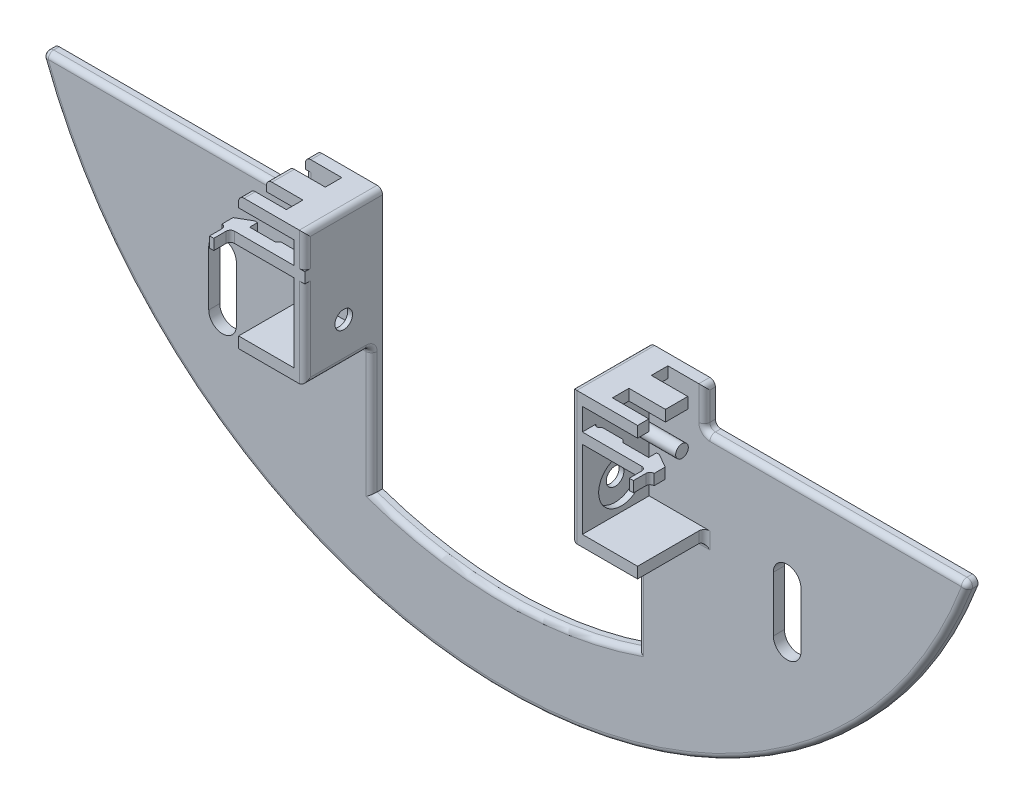
SolidWorks part; units mm, degrees
ref_plane "Front Plane" through (0, 0, 0) normal (0, 0, 1) x (1, 0, 0)
ref_plane "Top Plane" through (0, 0, 0) normal (0, 1, 0) x (1, 0, 0)
ref_plane "Right Plane" through (0, 0, 0) normal (1, 0, 0) x (0, 0, -1)
sketch "Sketch1" plane through (0, 0, 0) normal (0, 0, 1) x (1, 0, 0)
  line L0 (24.15, -30.4) -> (24.15, -23.3309)
  line L2 (24.15, -23.3309) -> (36.15, -23.3309)
  line L3 (-20.7971, -18) -> (20.7971, -18) construction
  line L4 (36.15, -23.3309) -> (36.15, -30.4)
  line L6 (-20.7971, -30.4) -> (20.7971, -30.4) construction
  line L7 (16, -30.4) -> (-16, -30.4) construction
  line L8 (0, -18) -> (0, -30.4) construction
  line L9 (-24.15, -30.4) -> (-24.15, -23.3309)
  line L10 (-24.15, -23.3309) -> (-36.15, -23.3309)
  line L11 (-36.15, -23.3309) -> (-36.15, -30.4)
  line L13 (36.15, -30.4) -> (84.1789, -30.4)
  line L14 (-36.15, -30.4) -> (-84.1789, -30.4)
  line L15 (-24.15, -30.4) -> (-24.15, -70.4771)
  line L16 (24.15, -30.4) -> (24.15, -70.4771)
  line L17 (20, -46.2619) -> (20, -34.4) construction
  circle A6 centre (0, 0) radius 89.5
  arc A7 (-84.1789, -30.4) -> (84.1789, -30.4) centre (0, 0) ccw
  arc A13 (-24.15, -70.4771) -> (24.15, -70.4771) centre (0, 0) ccw
  arc A39 (-7.5, 16.3631) -> (7.5, 16.3631) centre (0, 0) ccw construction
  point P13 (-65.8932, -25.0667)
  point P14 (0, -18)
  point P17 (0, -30.4)
  point P22 (65.8932, -25.0667)
  point P31 (20, -40.3309)
  dimension "D3" = 4.15
  dimension "irBeamUnitWidth" = 12
  dimension "D4" = 15
  dimension "irBeamUnitLEDDistanceFromBottom" = 17
  dimension "D1" = 26
extrude "Boss-Extrude1" add sketch "Sketch1" along normal blind 2
sketch "Sketch3" plane through (0, 0, 2) normal (0, 0, -1) x (-1, 0, 0)
  line L0 (26.15, -45.4309) -> (26.15, -25.3309)
  line L1 (26.15, -25.3309) -> (36.15, -25.3309)
  line L2 (24.15, -23.3309) -> (36.15, -23.3309) construction
  line L3 (24.15, -70.4771) -> (24.15, -23.3309) construction
  line L4 (24.15, -23.3309) -> (36.15, -23.3309)
  line L5 (24.15, -47.4309) -> (24.15, -23.3309)
  line L7 (36.15, -23.3309) -> (36.15, -30.4) construction
  line L8 (36.15, -23.3309) -> (36.15, -25.3309)
  line L9 (-36.15, -47.4309) -> (-24.15, -47.4309)
  line L10 (0, 0) -> (0, -125.7174) construction
  line L11 (26.15, -45.4309) -> (36.15, -45.4309)
  line L12 (36.15, -45.4309) -> (36.15, -47.4309)
  line L13 (36.15, -47.4309) -> (24.15, -47.4309)
  line L14 (-36.15, -45.4309) -> (-36.15, -47.4309)
  line L15 (-26.15, -45.4309) -> (-36.15, -45.4309)
  line L16 (-36.15, -23.3309) -> (-36.15, -25.3309)
  line L17 (-24.15, -47.4309) -> (-24.15, -23.3309)
  line L18 (-24.15, -23.3309) -> (-36.15, -23.3309)
  line L19 (-26.15, -25.3309) -> (-36.15, -25.3309)
  line L20 (-26.15, -45.4309) -> (-26.15, -25.3309)
  dimension "D1" = 2
  dimension "D2" = 2
  dimension "D3" = 2
  dimension "irBeamUnitLength" = 20.1
extrude "Boss-Extrude2" add sketch "Sketch3" against normal blind 12.1
sketch "Sketch4" plane through (26.15, 0, 0) normal (1, 0, 0) x (0, 0, -1)
  line L0 (-2, -30.4) -> (-2, -89.5) construction
  line L3 (-14.1, -25.3309) -> (-2, -25.3309) construction
  circle A0 centre (-7.05, -40.3809) radius 4.1
  dimension "irBeamUnitLEDMountDiameter" = 8.2
  dimension "irBeamUnitLEDDistanceFromBottom" = 15.05
  dimension "irBeamUnitWidth" = 5.05
extrude "Cut-Extrude1" cut sketch "Sketch4" against normal blind 1.12
sketch "Sketch5" plane through (25.03, 0, 0) normal (1, 0, 0) x (0, 0, -1)
  line L0 (-2, -30.4) -> (-2, -89.5) construction
  line L1 (-14.1, -25.3309) -> (-2, -25.3309) construction
  circle A0 centre (-7.05, -40.3809) radius 1.6
  dimension "irBeamUnitWidth" = 5.05
  dimension "irBeamUnitLEDDiameter" = 3.2
  dimension "irBeamUnitLEDDistanceFromBottom" = 15.05
extrude "Cut-Extrude2" cut sketch "Sketch5" against normal up to surface (49.18 mm away)
sketch "Sketch6" plane through (26.15, 0, 0) normal (1, 0, 0) x (0, 0, -1)
  line L1 (-14.1, -25.3309) -> (-2, -25.3309) construction
  line L2 (-2, -30.4) -> (-2, -25.3309) construction
  circle A0 centre (-7.05, -30.3809) radius 1.15
  dimension "irBeamUnitWidth" = 5.05
  dimension "irBeamUnitMountHoleDiameter" = 2.3
  dimension "irBeamUnitMountHoleDistanceFromBottom" = 5.05
extrude "Boss-Extrude3" add sketch "Sketch6" along normal blind 11
sketch "Sketch8" plane through (0, 0, 14.1) normal (0, 0, 1) x (1, 0, 0)
  line L0 (24.15, -47.4309) -> (24.15, -23.3309) construction
  line L1 (24.15, -31.2909) -> (24.15, -29.3609)
  line L2 (24.15, -29.3609) -> (39.15, -29.3609)
  line L3 (39.15, -29.3609) -> (39.15, -31.2909)
  line L4 (39.15, -31.2909) -> (24.15, -31.2909)
  line L5 (36.15, -25.3309) -> (26.15, -25.3309) construction
  dimension "irBeamUnitSideSlotsDistanceFromBottom" = 4.03
  dimension "irBeamUnitSlotWidth" = 1.93
  dimension "irBeamUnitHeight" = 15
extrude "Boss-Extrude4" add sketch "Sketch8" against normal blind 2
sketch "Sketch9" plane through (0, -31.2909, 0) normal (0, -1, 0) x (1, 0, 0)
  line L0 (36.15, 12.1) -> (36.15, 10.6566)
  line L1 (26.15, 12.1) -> (39.15, 12.1) construction
  line L2 (36.15, 10.6566) -> (36.65, 10.6566)
  line L3 (36.65, 10.6566) -> (39.15, 12.1)
  line L5 (26.15, 12.1) -> (31.51, 12.1)
  line L6 (31.51, 12.1) -> (31, 11.59)
  line L9 (36.15, 12.1) -> (39.15, 12.1)
  line L10 (26.15, 14.1) -> (26.15, 12.1) construction
  line L12 (26.15, 12.1) -> (26.15, 11.59)
  line L13 (31, 11.59) -> (27.2589, 11.59)
  line L14 (27.2589, 11.59) -> (26.9954, 11.8536)
  line L15 (26.9972, 12) -> (26.2772, 12) construction
  line L17 (26.15, 14.1) -> (39.15, 14.1) construction
  line L22 (38.4, 14.85) -> (38.4, 17.1)
  line L23 (37.65, 17.1) -> (38.4, 17.1)
  line L24 (37.65, 17.1) -> (37.65, 14.85)
  line L25 (36.9, 14.1) -> (39.15, 14.1)
  arc A0 (26.9954, 11.8536) -> (26.15, 11.59) centre (26.6418, 11.5) ccw
  arc A1 (39.15, 14.1) -> (38.4, 14.85) centre (39.15, 14.85) cw
  arc A2 (37.65, 14.85) -> (36.9, 14.1) centre (36.9, 14.85) cw
  dimension "D7" = 0.5
  dimension "D10" = 0.75
  dimension "D1" = 45
  dimension "D2" = 4.85
  dimension "D4" = 10
  dimension "D5" = 0.5
  dimension "D3" = 0.51
  dimension "D6" = 60
  dimension "D8" = 0.1
  dimension "D9" = 0.75
  dimension "D11" = 3
extrude "Boss-Extrude5" add sketch "Sketch9" against normal up to surface (1.93 mm away) up to face at (32.65, -29.3609, 13.1)
sketch "Sketch10" plane through (0, -25.3309, 0) normal (0, -1, 0) x (1, 0, 0)
  line L0 (36.15, 14.1) -> (36.15, 2) construction
  line L1 (36.15, 12.05) -> (36.15, 9.05)
  line L2 (36.15, 2) -> (29.54, 2)
  line L3 (36.15, 2) -> (26.15, 2) construction
  line L4 (29.54, 2) -> (29.54, 5)
  line L7 (26.15, 14.1) -> (26.15, 2) construction
  line L8 (29.54, 9.05) -> (36.15, 9.05)
  line L9 (29.54, 5) -> (36.15, 5)
  line L10 (36.15, 12.05) -> (29.54, 12.05)
  line L11 (29.54, 12.05) -> (29.54, 9.05)
  line L12 (36.15, 5) -> (36.15, 2)
  line L14 (36.15, 14.1) -> (26.15, 14.1) construction
  dimension "irBeamUnitHeight" = 3.39
  dimension "D2" = 3
  dimension "D3" = 3
  dimension "irBeamUnitMountingPlateThickness" = 2.05
extrude "Cut-Extrude3" cut sketch "Sketch10" against normal through all
fillet "Fillet1" radius 1 24 edges at (36.15, -23.3309, 1) (-60.1645, -30.4, 2) (24.15, -23.3309, 7.05) (36.15, -30.4, 1) (84.1789, -30.4, 1) (-84.1789, -30.4, 1) (-36.15, -30.4, 1) (-36.15, -23.3309, 7.05) (-24.15, -23.3309, 7.05) (0, -89.5, 2) (60.1645, -30.4, 2) (36.15, -26.8655, 2) (-36.15, -27.8655, 2) (-24.15, -35.3809, 14.1) (-24.15, -47.4309, 8.05) (-30.15, -47.4309, 2) (-36.15, -46.4309, 2) (0, -74.5, 2) (-24.15, -58.954, 2) (24.15, -58.954, 2) (24.15, -35.3809, 14.1) (24.15, -47.4309, 8.05) (36.15, -46.4309, 2) (30.15, -47.4309, 2)
hole_wizard "Ø5.0mm Dowel Hole1" positions "Sketch16" profile "Sketch17" hole size "Ø5.0" standard "ANSI Metric" end condition through all
sketch "Sketch16" plane through (0, 0, -31.1) normal (0, 0, -1) x (-1, 0, 0)
  point P0 (-51.1598, -51.1598)
  point P3 (51.1598, -51.1598)
  point P6 (51.1598, 51.1598)
  point P9 (-51.1598, 51.1598)
sketch "Sketch17" plane through (51.1598, -51.1598, -31.1) normal (1, 0, 0) x (0, 1, 0)
  line L0 (0, 0) -> (0, 48.2)
  line L1 (0, 48.2) -> (2.5, 48.2)
  line L2 (2.5, 48.2) -> (2.5, 0)
  line L3 (2.5, 0) -> (0, 0)
  line L4 (0, -6.35) -> (0, 107.95) construction
  dimension "Thru Hole Dia." = 5
  dimension "Thru Hole Depth" = 48.2
sketch "Sketch13" plane through (0, 0, 2) normal (0, 0, 1) x (1, 0, 0)
  line L0 (51.1598, -46.1598) -> (51.1598, -56.1598) construction
  line L1 (53.6598, -46.1598) -> (53.6598, -56.1598)
  line L2 (48.6598, -46.1598) -> (48.6598, -56.1598)
  arc A0 (53.6598, -46.1598) -> (48.6598, -46.1598) centre (51.1598, -46.1598) ccw
  arc A1 (48.6598, -56.1598) -> (53.6598, -56.1598) centre (51.1598, -56.1598) ccw
  circle A6 centre (51.1598, -51.1598) radius 2.5 construction
  point P2 (51.1598, -51.1598)
  dimension "irBeamUnitMountingPlateAdjustmentSlotLength" = 10
extrude "Cut-Extrude4" cut sketch "Sketch13" against normal through all
mirror "Mirror1" about plane through (0, 0, 0) normal (1, 0, 0) of "Cut-Extrude4", "Cut-Extrude2", "Boss-Extrude3", "Boss-Extrude4", "Boss-Extrude5", "Cut-Extrude3", "Cut-Extrude1"
equation "\"D1@Sketch1\"=\"motorMountOffset\"-\"hopperBaseLipOverhang\"+1"
equation "\"D3@Sketch1\"=(\"irBeamUnitLEDDomeSectionDiameter\"/2) + \"irBeamUnitLEDFlatSectionHeight\" + 2mm"
equation "\"pelletWidth\"= 13mm'The Width of the pellet to be dispensed"
equation "\"pelletLength\"= 26mm'The length of the pellet to be dispensed"
equation "\"pelletThickness\"= 13mm'The Thickness of the pellet to be dispensed"
equation "\"pelletRadius\"= 10mm'The roundness / radius of the pellet to be dispensed"
equation "\"rotatingPlateDiameter\"= 100mm'the diameter of the rotating plate"
equation "\"rotatingPlateHeight\"= (\"pelletThickness\"*0.9)'The thickness of the rotating plate"
equation "\"rotatingPlateDiameterAllowance\"= 0.5mm'Allowance around the edge of the rotating plate"
equation "\"rotatingPlatePelletSlotLength\"= \"pelletLength\"*1.3'The length of the slot where a pellet will be captured"
equation "\"rotatingPlatePelletSlotWidth\"= \"pelletWidth\"*1.3'The width of the slot where a pellet will be captured"
equation "\"rotatingPlateNumberOfPelletSlots\"= ( (2*pi*(\"rotatingPlateDiameter\"/2)) / ((\"rotatingPlatePelletSlotLength\"*1.1)*3) )'The maximum number of pellet slots allows in the rotating plate for proper spacing"
equation "\"rotatingPlateAgitatorDiameter\"= ( \"rotatingPlateDiameter\"-((\"pelletWidth\"*1.3)*2.5) )'The diameter of the \"agitator\" section of the rotating plate"
equation "\"rotatingPlateAgitatorHeight\"= 80mm'The height of the \"agitator\" section of the rotating plate"
equation "\"rotatingPlateAgitatorTopRoundingRadius\"= 6mm'The rounding radius of the top of the \"agitator\" section of the rotating plate"
equation "\"rotatingPlateAgitatorBladeThickness\"= 4mm'The thickness of the blade on the \"agitator\" section of the rotating plate"
equation "\"rotatingPlateAgitatorBladeDistance\"= ( (\"rotatingPlateAgitatorDiameter\"+ 20mm) - (\"rotatingPlateAgitatorDiameter\") )'The distance offset of the blade from the surface of the \"agitator\" section of the rotating plate"
equation "\"rotatingPlateAgitatorBladeBottomGap\"= ( \"pelletThickness\"*1.2 )'The gap between the bottom of the blade and the base of the plate on the \"agitator\" section of the rotating plate"
equation "\"rotatingPlateAgitatorBladesNumber\"= ( 3 )'The number of blades on the \"agitator\" section of the rotating plate"
equation "\"hopperBaseInnerDiameter\"= (\"rotatingPlateDiameter\") + (\"rotatingPlateDiameterAllowance\"*2)'Diameter of the Base of the hopper where it meets the motor mount + rotating plate"
equation "\"hopperBaseOuterDiameter\"= (\"hopperBaseInnerDiameter\" + (\"hopperTankWallThickness\"*2) + 60mm)'Diameter of the Base of the hopper where it meets the motor mount + rotating plate"
equation "\"hopperBaseChamferAngle\"= 60deg'Angle of the chamfer of the Hopper base Toward the plate"
equation "\"hopperBaseLipOverhang\"= 5mm'The overhang amount of the hopper base lip"
equation "\"hopperBaseLipDepth\"= 5mm'The depth of the hopper base's overhang lip"
equation "\"hopperBaseLockNotchWidth\"= 10mm'The width of the hopper base \"lock\" notch to prevent rotation"
equation "\"hopperBaseLockNotchHeight\"= 10mm'The height of the hopper base \"lock\" notch to prevent rotation"
equation "\"hopperBaseRearNotchHeight\"= 8mm'The height of the rear snap-lock notch on the hopper base"
equation "\"hopperBaseRearNotchWidth\"= 8mm'The width of the rear snap-lock notch on the hopper base"
equation "\"hopperTankWallThickness\"= 5mm'The wall thickness of the hopper tank where pellet reserve will be stored"
equation "\"hopperTankDiameter\"= ( \"rotatingPlateDiameter\"*1.8 )'**Must be greater than \"rotatingPlateDiameter\" -- The inner diameter of the hopper tank where pellet reserve will be stored"
equation "\"hopperTankHeight\"= 200mm'The height of the hopper tank where pellet reserve will be stored"
equation "\"hopperTankCoverThickness\"= 10mm'The thickness of the Hopper Tank's cover"
equation "\"hopperTankCoverHandleLength\"= 60mm'The length of the handles on the hopper tank cover"
equation "\"hopperTankCoverHandleWidth\"= 20mm'The width of the handles on the hopper tank cover, defined as the offset from the cover's main edge"
equation "\"motorMountOffset\"= 30mm'The distance offset of the motor mount part from the hopper tank's outer edge"
equation "\"motorMountHeight\"= (\"motorHeight\" + \"motorFacePlateThickness\" + 0mm)'The height / thickness of the motor mount part"
equation "\"motorMountPelletThroughHoleLength\"= 40mm'The length of the pellet throughhole that routes through the motor mount and other parts"
equation "\"motorMountPelletThroughHoleWidth\"= 20mm'The width of the pellet throughhole that routes through the motor mount and other parts"
equation "\"motorDiameter\"= 35mm'The Diameter of the main motor unit"
equation "\"motorHeight\"= 13.4mm'The height of the main motor unit"
equation "\"motorConnectorWidth\"= 10mm'The width of the motor's electrical cable connector"
equation "\"motorConnectorLength\"= 8mm'The length of the motor's electrical cable connector"
equation "\"motorConnectorHeight\"= 5mm'The height of the motor's electrical cable connector"
equation "\"motorFacePlateLength\"= 50mm'The length of the motor faceplate"
equation "\"motorFacePlateWidth\"= 10mm'The width of the motor faceplate"
equation "\"motorFacePlateThickness\"= 1mm'The thickness of the motor faceplate"
equation "\"motorFacePlateCenterRadius\"= 20mm'The rounding radius of the motor faceplate center"
equation "\"motorFacePlateEndRadius\"= 10mm'The rounding radius of the motor faceplate ends"
equation "\"motorFacePlateMountingHoleDiameter\"= 6mm'The diameter of the motor faceplate's mounting holes"
equation "\"motorFacePlateMoutingHoleDistanceBetweenHoles\"= 42mm'The distance between the center of the mounting holes"
equation "\"motorSpindleDiameter\"= 2mm'The diameter of the motor spindle"
equation "\"motorSpindleFlatFaceLength\"= 1.5mm'The length of the flat face of the motor spindle"
equation "\"motorSpindleHeight\"= 9mm'The height of the motor spindle from the face of the motor"
equation "\"motorSpindleMountDiameter\"= 12mm'The diameter of the raised mount section of the motor where the spindle is attached"
equation "\"motorSpindleMountHeight\"= 1.5mm'The height of the raised mount section of the motor where the spindle is attached"
equation "\"irBeamUnitLength\"=20mm'The legth of the IR beam unit"
equation "\"irBeamUnitWidth\"=10mm'The width of the IR beam unit"
equation "\"irBeamUnitHeight\"=8mm'The height of the IR beam unit"
equation "\"irBeamUnitSlotWidth\"=2.03mm'The width of the slots on the outside of the IR beam unit"
equation "\"irBeamUnitSlotDepth\"=0.76mm'The depth of the slots on the outside of the IR beam unit"
equation "\"irBeamUnitSideSlotsDistanceFromBottom\"=3.98mm'The distance of the side slots on the outside of the IR beam unit from the bottom edge of the unit"
equation "\"irBeamUnitMountHoleDistanceFromBottom\"=5mm'The distance of the center mounting throughhole of the IR beam unit from the bottom edge of the unit"
equation "\"irBeamUnitMountHoleDiameter\"=2.40mm'The diameter of the center mounting throughhole of the IR beam unit"
equation "\"irBeamUnitMountHoleChamferDiameter\"=5.30mm'The diameter of the chamfer of the center mounting throughole of the IR beam unit"
equation "\"irBeamUnitMountHoleChamferDepth\"=2.65mm'The depth of the chamfer of the center mounting throughole of the IR beam unit"
equation "\"irBeamUnitLEDDistanceFromBottom\"=15mm'The distance of the center of the LED from the bottom edge of the IR beam unit"
equation "\"irBeamUnitLEDMountDiameter\"=8mm'The diameter of the LED mounting base of the IR beam unit"
equation "\"irBeamUnitLEDMountHeight\"=1.02mm'The height of the LED mounting base of the IR beam unit"
equation "\"irBeamUnitLEDDiameter\"=3.00mm'The diameter of the LED of the IR beam unit"
equation "\"irBeamUnitLEDFlatSectionHeight\"=0.65mm'The height of the \"flat\" section of the LED of the IR beam unit"
equation "\"irBeamUnitLEDDomeSectionDiameter\"=\"irBeamUnitLEDDiameter\"'The diameter of the \"domed\" section of the LED of the IR beam unit"
equation "\"irBeamUnitMountingPlateThickness\"=2mm'The thickness of the IR beam unit mounting plate"
equation "\"generalFittingTolerance\"= 0.1mm'The general fitting tolerance between contacting parts"
equation "\"irBeamUnitWidth@Sketch1\" = \"irBeamUnitWidth\" +  ( \"irBeamUnitMountingPlateThickness\" * 1 ) "
equation "\"irBeamUnitLEDDistanceFromBottom@Sketch1\" = \"irBeamUnitLEDDistanceFromBottom\" + \"irBeamUnitMountingPlateThickness\""
equation "\"D1@Sketch3\"=\"irBeamUnitMountingPlateThickness\""
equation "\"D2@Sketch3\"=\"irBeamUnitMountingPlateThickness\""
equation "\"D3@Sketch3\"=\"irBeamUnitMountingPlateThickness\""
equation "\"irBeamUnitLength@Sketch3\" = \"irBeamUnitLength\" + \"generalFittingTolerance\""
equation "\"D1@Boss-Extrude2\"=\"irBeamUnitWidth\"+\"generalFittingTolerance\"+\"irBeamUnitMountingPlateThickness\""
equation "\"irBeamUnitLEDMountDiameter@Sketch4\" = \"irBeamUnitLEDMountDiameter\" +  ( \"generalFittingTolerance\" * 2 ) "
equation "\"irBeamUnitLEDDistanceFromBottom@Sketch4\" = \"irBeamUnitLEDDistanceFromBottom\" +  ( \"generalFittingTolerance\" / 2 ) "
equation "\"D1@Cut-Extrude1\"=\"irBeamUnitLEDMountHeight\"+\"generalFittingTolerance\""
equation "\"irBeamUnitLEDDiameter@Sketch5\" = \"irBeamUnitLEDDiameter\" +  ( \"generalFittingTolerance\" * 2 ) "
equation "\"D1@Boss-Extrude3\"=\"irBeamUnitHeight\"+3mm"
equation "\"D1@Boss-Extrude1\"=\"irBeamUnitMountingPlateThickness\""
equation "\"irBeamUnitHeight@Sketch8\" = \"irBeamUnitHeight\" + \"irBeamUnitMountingPlateThickness\" + 5"
equation "\"irBeamUnitSideSlotsDistanceFromBottom@Sketch8\" = \"irBeamUnitSideSlotsDistanceFromBottom\" +  ( \"generalFittingTolerance\" / 2 ) "
equation "\"irBeamUnitSlotWidth@Sketch8\" = \"irBeamUnitSlotWidth\" - \"generalFittingTolerance\""
equation "\"irBeamUnitWidth@Sketch4\" =  ( \"irBeamUnitWidth\" / 2 )  +  ( \"generalFittingTolerance\" / 2 ) "
equation "\"irBeamUnitWidth@Sketch5\" =  ( \"irBeamUnitWidth\" / 2 )  +  ( \"generalFittingTolerance\" / 2 ) "
equation "\"irBeamUnitLEDDistanceFromBottom@Sketch5\" = \"irBeamUnitLEDDistanceFromBottom\" +  ( \"generalFittingTolerance\" / 2 ) "
equation "\"irBeamUnitMountHoleDiameter@Sketch6\" = \"irBeamUnitMountHoleDiameter\" - \"generalFittingTolerance\""
equation "\"irBeamUnitMountHoleDistanceFromBottom@Sketch6\" = \"irBeamUnitMountHoleDistanceFromBottom\" +  ( \"generalFittingTolerance\" / 2 ) "
equation "\"irBeamUnitWidth@Sketch6\" =  ( \"irBeamUnitWidth\" / 2 )  +  ( \"generalFittingTolerance\" / 2 ) "
equation "\"D1@Boss-Extrude4\"=\"irBeamUnitMountingPlateThickness\""
equation "\"irBeamUnitSlotLength\"=5.10mm'The length of the slots of the outside of the IR beam unit"
equation "\"irBeamUnitSlotChamferAngle\"=45deg'The angle of the \"end\" of the slot on the outside of the IR beam unit"
equation "\"D1@Sketch9\"=\"irBeamUnitSlotChamferAngle\""
equation "\"D2@Sketch9\"=\"irBeamUnitSlotLength\"-0.25"
equation "\"D4@Sketch9\"=\"irBeamUnitWidth\""
equation "\"D3@Sketch9\"=\"irBeamUnitSlotDepth\"-0.25"
equation "\"irBeamUnitHeight@Sketch10\" = \"irBeamUnitHeight\" - 4.61mm"
equation "\"irBeamUnitMountingPlateThickness@Sketch10\" = \"irBeamUnitMountingPlateThickness\" +  ( \"generalFittingTolerance\" / 2 ) "
equation "\"irBeamUnitMountingPlateAdjustmentSlotLength\"=10mm'The length of the variable/adjustable mounting slot of the IR beam unit mounting plate"
equation "\"irBeamUnitMountingPlateAdjustmentSlotLength@Sketch13\" = \"irBeamUnitMountingPlateAdjustmentSlotLength\""
equation "\"hopperBasePelletBlockerMountingSlotWidth\"= 5mm'The width of the pellet blocker mounting slot on the hopper base"
equation "\"hopperBasePelletBlockerMountingSlotOffsetFromTopOfChamfer\"= 15mm'The distance offset of the top of the pellet blocker mounting slot from the top of the hopper base chamfer"
equation "\"hopperBasePelletBlockerMountingSlotOffsetFromBottomOfChamfer\"= 10mm'The distance offset of the bottom of the pellet blocker mounting slot from the bottom of the hopper base chamfer"
equation "\"pelletBlockerBaseWidth\"= (\"rotatingPlatePelletSlotWidth\"+\"rotatingPlateDiameterAllowance\")*1.1'The width of the base of the pellet blocker where it meets the rotating plate & pellet slot"
equation "\"pelletBlockerBaseLength\"= \"rotatingPlatePelletSlotLength\"*1.1'The length of the base of the pellet blocker where it meets the rotating plate & pellet slot"
equation "\"pelletBlockerBaseRoundingRadius\"= \"pelletWidth\"*0.5'The rounding radius of the base of the pellet blocker where it meets the rotating plate & pellet slot"
equation "\"pelletBlockerBaseHeight\"= \"rotatingPlateAgitatorBladeBottomGap\"*0.75'The height of the base of the pellet blocker where it meets the rotating plate & pellet slot"
equation "\"pelletBlockerNeckLength\"= 50mm'The length of the neck of the pellet blocker"
equation "\"pelletBlockerNeckTopRoundingRadius\"=2mm'The rounding radius of the top of the neck of the pellet blocker"
equation "\"pelletOutletTrackMountingPlateThickness\"= 2mm'The thickness of the Pellet Outlet Track Mounting Plate"
equation "\"pelletOutletTrackMountingPlateHingeHeight\"= (\"irBeamUnitWidth\" + \"irBeamUnitMountingPlateThickness\" + 2mm )'The height of the bottom of the hinge of the Pellet Outlet Mounting Plate"
equation "\"pelletOutletTrackMountingPlateHingeDiameter\"= 6mm'The inner diameter of the hinge on the Pellet Outlet Mounting Plate"
equation "\"pelletOutletTrackMountingPlateHingeOffsetFromHoleDistance\"= (\"pelletOutletTrackMountingPlateHingeDiameter\" + \"pelletOutletTrackMountingPlateThickness\" + 4mm)'The distance offset of the hinge of the Pellet Outlet Mounting Plate from the plate's mounting hole position"
equation "\"pelletOutletTrackHingeWidth\"= 10mm'The width of the pellet outlet track's hinge which mates with the hinge on the mounting plate"
equation "\"pelletOutletTrackHingeOffsetFromIRBeamUnitEdge\"= 6mm'The distance offset of the pelletOutletTrack's mating hinge from the edge of the IR Beam Unit"
equation "\"pelletOutletTrackEndingWidth\"= 50mm'The width of the pellet outlet Track at the end of the Track"
equation "\"pelletOutletTrackEndingLength\"= 30mm'The length of pellet outlet Track at the end of the Track"
equation "\"pelletOutletTrackWallHeight\"= 15mm'The height of the side walls of the pellet outlet Track"
equation "\"pelletOutletTrackThickness\"= 2mm'The thickness of the pellet outlet Track"
equation "\"baseStandMountingFaceHeight\"= 10mm'The height / thickness of the mounting face between the Base Stand and the Motor Mount parts"
equation "\"baseStandOpeningAngle\"= 55deg'The angle of the opening in the front of the Base Stand to allow for unobstructed pellet outlet"
equation "\"baseStandWallThickness\"= 10mm'The wall thickness of the Base Stand"
equation "\"baseStandHeight\"= 100mm'The overall height of the Base Stand part"
equation "\"baseStandFootDiameterOffset\"= 40mm'The distance offset of the Base Stand's foot ring"
equation "\"baseStandFootHeight\"= 20mm'The height / thickness of the Base Stand's foot ring"
